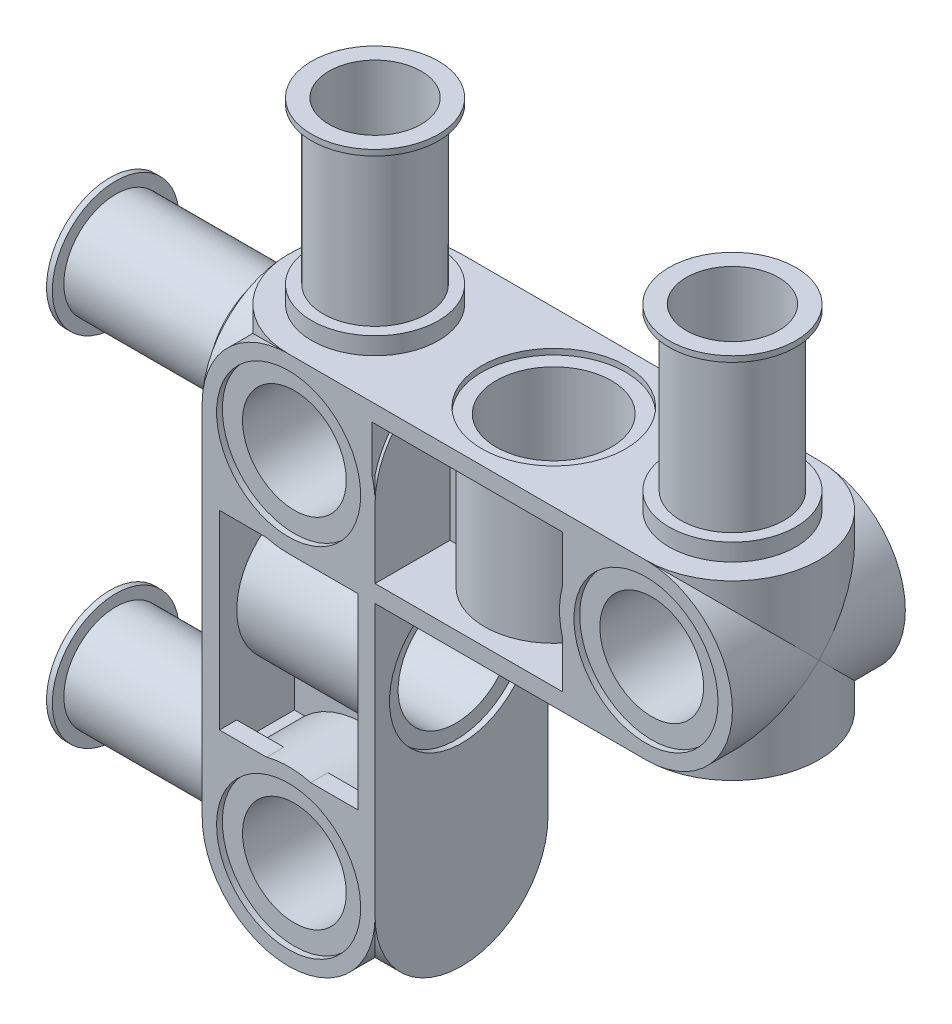
SolidWorks part; units mm, degrees
material "PVC Rigid"
ref_plane "Front Plane" through (0, 0, 0) normal (0, 0, 1) x (1, 0, 0)
ref_plane "Top Plane" through (0, 0, 0) normal (0, 1, 0) x (1, 0, 0)
ref_plane "Right Plane" through (0, 0, 0) normal (1, 0, 0) x (0, 0, -1)
sketch "Sketch1" plane through (0, 0, 0) normal (0, 1, 0) x (1, 0, 0)
  line L0 (-19.2625, 0) -> (26.4221, 0) construction
  line L1 (-7.874, 3.81) -> (7.874, 3.81)
  line L2 (0, 0) -> (0, 11.754) construction
  line L3 (7.874, -3.81) -> (-7.874, -3.81)
  circle A0 centre (-7.874, 0) radius 2.54 construction
  circle A1 centre (0, 0) radius 2.54 construction
  circle A2 centre (7.874, 0) radius 2.54 construction
  arc A3 (7.874, -3.81) -> (7.874, 3.81) centre (7.874, 0) ccw
  arc A4 (-7.874, 3.81) -> (-7.874, -3.81) centre (-7.874, 0) ccw
  dimension "D3" = 5.08
  dimension "D4" = 7.62
  dimension "D1" = 7.874
  dimension "D2" = 7.874
extrude "Extrude1" add sketch "Sketch1" along normal blind 3.81
sketch "Sketch2" plane through (0, 0, 0) normal (0, -1, 0) x (1, 0, 0)
  circle A0 centre (0, 0) radius 2.794
  dimension "D1" = 5.588
extrude "Cut-Extrude1" cut sketch "Sketch2" against normal blind 0.254
sketch "Sketch3" plane through (0, 0, 0) normal (0, -1, 0) x (1, 0, 0)
  circle A0 centre (7.874, 0) radius 2.794
  circle A1 centre (-7.874, 0) radius 2.794
  arc A2 (-7.874, 3.81) -> (-7.874, -3.81) centre (-7.874, 0) ccw construction
  arc A3 (7.874, -3.81) -> (7.874, 3.81) centre (7.874, 0) ccw construction
  dimension "D1" = 5.588
extrude "Extrude2" add sketch "Sketch3" along normal blind 0.762
sketch "Sketch5" plane through (0, -0.762, 0) normal (0, -1, 0) x (1, 0, 0)
  circle A0 centre (7.874, 0) radius 2.794 construction
  circle A1 centre (7.874, 0) radius 2.286
  circle A2 centre (-7.874, 0) radius 2.794 construction
  circle A3 centre (7.874, 0) radius 2.032
  circle A4 centre (-7.874, 0) radius 2.286
  circle A8 centre (-7.874, 0) radius 2.032
  dimension "D2" = 4.572
  dimension "D1" = 4.064
extrude "Extrude4" add sketch "Sketch5" along normal blind 7.112
sketch "Sketch6" plane through (0, -7.874, 0) normal (0, -1, 0) x (1, 0, 0)
  circle A1 centre (-7.874, 0) radius 2.032 construction
  circle A3 centre (7.874, 0) radius 2.032 construction
  circle A4 centre (-7.874, 0) radius 2.794 construction
  circle A5 centre (7.874, 0) radius 2.794 construction
  circle A6 centre (-7.874, 0) radius 2.794
  circle A7 centre (7.874, 0) radius 2.794
  circle A8 centre (7.874, 0) radius 2.032
  circle A9 centre (-7.874, 0) radius 2.032
extrude "Extrude5" add sketch "Sketch6" against normal blind 0.254
sketch "Sketch7" plane through (0, 0, -3.81) normal (0, 0, -1) x (-1, 0, 0)
  line L0 (-7.874, 3.81) -> (7.874, 3.81) construction
  line L2 (-7.874, 0) -> (7.874, 0) construction
  line L3 (-7.874, 0) -> (7.874, 0)
  line L4 (-7.874, 3.81) -> (7.874, 3.81)
  line L5 (-7.874, 3.81) -> (-11.684, 3.81)
  line L6 (7.874, 3.81) -> (11.684, 3.81)
  arc A0 (-11.684, 3.81) -> (-7.874, 0) centre (-7.874, 3.81) ccw
  arc A1 (7.874, 0) -> (11.684, 3.81) centre (7.874, 3.81) ccw
extrude "Extrude6" add sketch "Sketch7" against normal blind 7.62
sketch "Sketch8" plane through (0, 3.81, 0) normal (0, 1, 0) x (1, 0, 0)
  circle A0 centre (-7.874, 0) radius 2.54 construction
  circle A1 centre (0, 0) radius 2.54 construction
  circle A2 centre (7.874, 0) radius 2.54 construction
  circle A3 centre (-7.874, 0) radius 2.54 construction
  circle A4 centre (0, 0) radius 2.54
  circle A5 centre (7.874, 0) radius 2.54 construction
extrude "Cut-Extrude2" cut sketch "Sketch8" against normal blind 3.556
sketch "Sketch9" plane through (0, 0, 3.81) normal (0, 0, 1) x (1, 0, 0)
  circle A0 centre (7.874, 3.81) radius 2.286
  circle A1 centre (-7.874, 3.81) radius 2.286
  dimension "D1" = 4.572
extrude "Cut-Extrude3" cut sketch "Sketch9" against normal through all
sketch "Sketch10" plane through (0, 0, 3.81) normal (0, 0, 1) x (1, 0, 0)
  circle A0 centre (7.874, 3.81) radius 3.175
  circle A1 centre (-7.874, 3.81) radius 3.175
  dimension "D1" = 6.35
extrude "Cut-Extrude4" cut sketch "Sketch10" against normal blind 0.254
mirror "Mirror2" about plane through (0, 0, 0) normal (0, 0, 1) of "Cut-Extrude4"
sketch "Sketch11" plane through (0, 3.81, 0) normal (0, 1, 0) x (1, 0, 0)
  line L0 (-5.08, -0.508) -> (-5.08, -3.048)
  line L1 (5.08, 0.508) -> (5.08, 3.048)
  line L2 (5.08, -3.048) -> (5.08, -0.508)
  line L23 (4.699, 3.81) -> (-4.699, 3.81) construction
  line L24 (-5.809, 0) -> (6.5071, 0) construction
  line L25 (-5.08, 0.508) -> (-3.0054, 0.508)
  line L26 (-5.809, 0.508) -> (6.5071, 0.508) construction
  line L27 (-5.08, -0.508) -> (-3.0054, -0.508)
  line L28 (-5.809, -0.508) -> (6.5071, -0.508) construction
  line L29 (-4.699, -3.81) -> (4.699, -3.81) construction
  line L30 (-4.191, -3.81) -> (4.191, -3.81)
  line L31 (3.0054, -0.508) -> (5.08, -0.508)
  line L32 (-4.191, -3.048) -> (-4.191, -3.302)
  line L33 (-4.191, -3.302) -> (4.191, -3.302)
  line L34 (4.191, -3.302) -> (4.191, -3.048)
  line L35 (4.191, -3.048) -> (5.08, -3.048)
  line L36 (5.08, -3.048) -> (5.08, 3.048)
  line L37 (4.191, 3.302) -> (-4.191, 3.302)
  line L38 (4.191, 3.81) -> (-4.191, 3.81)
  line L39 (-4.191, 3.302) -> (-4.191, 3.048)
  line L40 (-5.08, 3.048) -> (-5.08, -3.048)
  line L41 (-5.08, -3.048) -> (-4.191, -3.048)
  line L42 (-4.191, -3.048) -> (-4.191, -3.81)
  line L43 (3.0054, 0.508) -> (5.08, 0.508)
  line L44 (4.191, -3.81) -> (4.191, -3.048)
  line L45 (4.191, -3.048) -> (5.08, -3.048)
  line L47 (-4.191, 3.81) -> (-4.191, 3.048)
  line L49 (-4.191, 3.048) -> (-5.08, 3.048)
  line L50 (-5.08, 3.048) -> (-5.08, 0.508)
  line L51 (-5.08, -3.048) -> (-4.191, -3.048)
  line L65 (-4.191, 3.048) -> (-5.08, 3.048)
  line L70 (5.08, 3.048) -> (4.191, 3.048)
  line L71 (5.08, 3.048) -> (4.191, 3.048)
  line L72 (4.191, 3.048) -> (4.191, 3.302)
  line L73 (4.191, 3.048) -> (4.191, 3.81)
  circle A5 centre (0, 0) radius 3.048
  arc A6 (-3.0054, -0.508) -> (3.0054, -0.508) centre (0, 0) ccw
  arc A8 (3.0054, 0.508) -> (-3.0054, 0.508) centre (0, 0) ccw
  dimension "D1" = 0.508
  dimension "D2" = 0.508
  dimension "D3" = 0.508
  dimension "D4" = 0.508
extrude "Cut-Extrude6" cut sketch "Sketch11" against normal blind 3.048
sketch "Sketch13" plane through (0, 0.254, 0) normal (0, 1, 0) x (1, 0, 0)
  circle A1 centre (0, 0) radius 2.54
  circle A2 centre (0, 0) radius 2.54
  dimension "D1" = 0
extrude "Cut-Extrude7" cut sketch "Sketch13" against normal through all
sketch "Sketch14" plane through (0, 0, 0) normal (0, -1, 0) x (1, 0, 0)
  circle A0 centre (0, 0) radius 3.175
  dimension "D1" = 6.35
extrude "Cut-Extrude8" cut sketch "Sketch14" against normal blind 0.254
sketch "Sketch17" plane through (0, 0, 3.81) normal (0, 0, 1) x (1, 0, 0)
  line L0 (-4.064, 3.81) -> (-4.699, 3.81)
  line L1 (-11.049, 3.81) -> (-11.684, 3.81)
  arc A0 (-11.684, 3.81) -> (-4.064, 3.81) centre (-7.874, 3.81) ccw
  arc A1 (-11.049, 3.81) -> (-4.699, 3.81) centre (-7.874, 3.81) ccw construction
  arc A2 (-11.049, 3.81) -> (-4.699, 3.81) centre (-7.874, 3.81) ccw
  dimension "D1" = 3.81
extrude "Extrude8" add sketch "Sketch17" against normal blind 7.112
mirror "Mirror3" about plane through (0, 0, 0) normal (1, 0, 0) of "Extrude8"
mirror "Mirror1" of bodies 118 111
sketch "Sketch18" plane through (0, 0, 3.81) normal (0, 0, 1) x (1, 0, 0)
  line L0 (-14.1345, 0) -> (15.6326, 0)
extrude "Extrude10" cut sketch "Sketch18" against normal through all and the other way through all flip side to cut
pattern_circular "CirPattern1" count 2 every 90 about axis through (-7.874, 3.81, 0) along (0, 0, 1) of bodies 121
sketch "Sketch19" plane through (0, 0, 3.81) normal (0, 0, 1) x (1, 0, 0)
  point P0 (-7.874, 3.81)
ref_plane "Plane1" through (-7.874, 0, 0) normal (1, 0, 0) x (0, 0, -1)
mirror "Mirror4" about plane through (-7.874, 0, 0) normal (1, 0, 0) of bodies 122
delete or keep bodies "Body-Delete1" type delete bodies bodies 122
combine bodies "Combine1" operation type add bodies to combine 121 123
